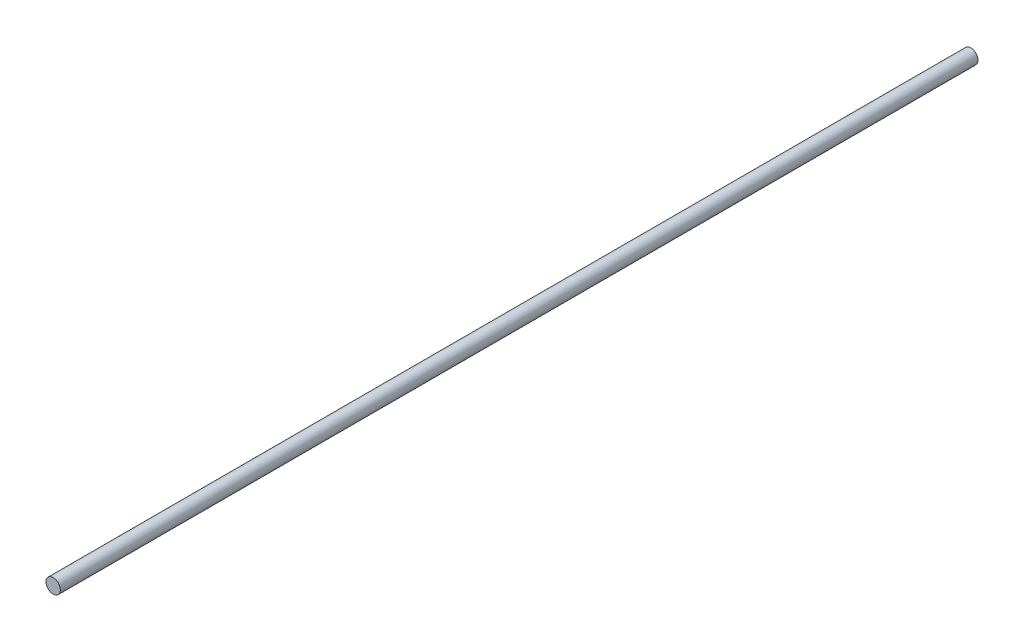
SolidWorks part; units mm, degrees
material "1023 Carbon Steel Sheet (SS)"
ref_plane "Front Plane" through (0, 0, 0) normal (0, 0, 1) x (1, 0, 0)
ref_plane "Top Plane" through (0, 0, 0) normal (0, 1, 0) x (1, 0, 0)
ref_plane "Right Plane" through (0, 0, 0) normal (1, 0, 0) x (0, 0, -1)
sketch "Sketch1" plane through (0, 0, 0) normal (0, 0, 1) x (1, 0, 0)
  circle A0 centre (0, 0) radius 6.35
  dimension "D1" = 12.7
extrude "Boss-Extrude1" add sketch "Sketch1" along normal mid plane 812.8
